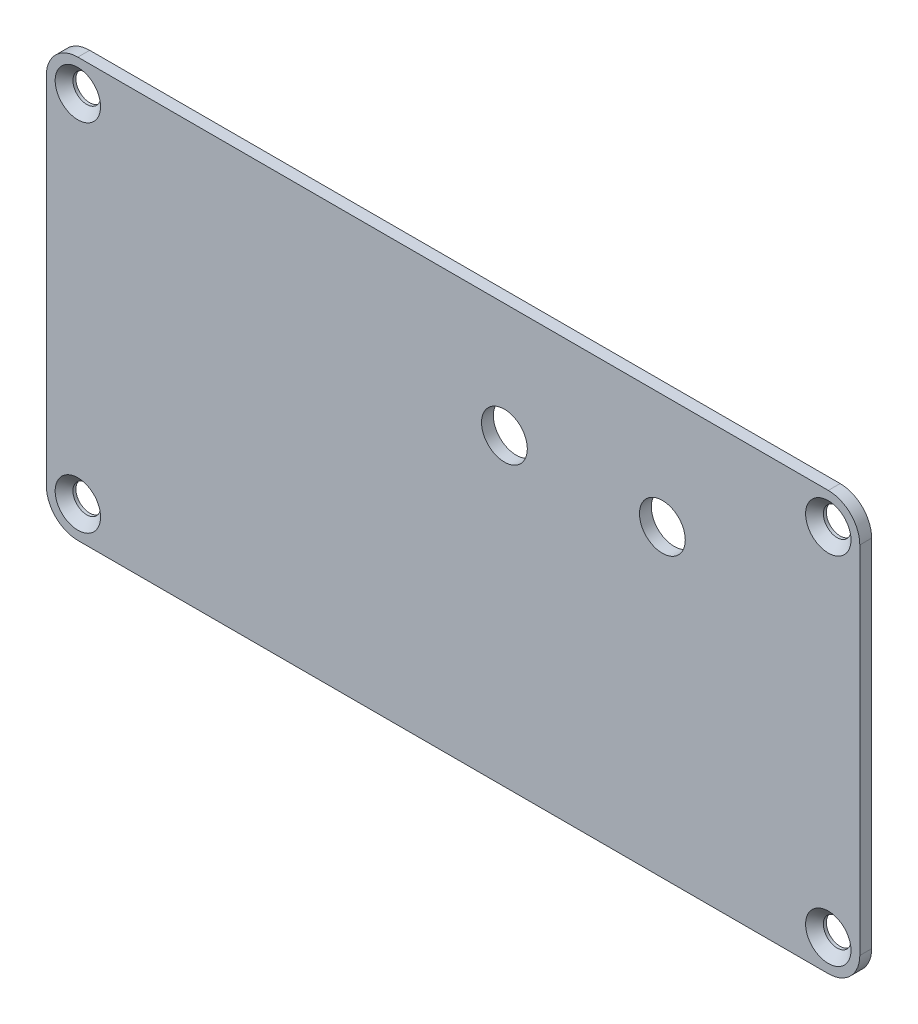
SolidWorks part; units mm, degrees
ref_plane "Plan de face" through (0, 0, 0) normal (0, 0, 1) x (1, 0, 0)
ref_plane "Plan de dessus" through (0, 0, 0) normal (0, 1, 0) x (1, 0, 0)
ref_plane "Plan de droite" through (0, 0, 0) normal (1, 0, 0) x (0, 0, -1)
ref_plane "Plan1" through (0, 0, -0.75) normal (0, 0, -1) x (-1, 0, 0)
sketch "Esquisse1" plane through (0, 0, -0.75) normal (0, 0, -1) x (-1, 0, 0)
  line L0 (-51.5, -26.5) -> (51.5, -26.5)
  line L1 (51.5, -26.5) -> (51.5, 26.5)
  line L2 (51.5, 26.5) -> (-51.5, 26.5)
  line L3 (-51.5, 26.5) -> (-51.5, -26.5)
extrude "Boss.-Extru.1" add sketch "Esquisse1" against normal blind 1.5
hole_wizard "Fraisage pour vis à tête fraisée M31" positions "Esquisse3" profile "Esquisse2" countersink size "M3" standard "Ansi Metric"
sketch "Esquisse3" plane through (0, 0, 0.75) normal (0, 0, 1) x (1, 0, 0)
  point P0 (-47.51, 22.5)
  point P1 (47.51, 22.5)
  point P2 (47.51, -22.5)
  point P3 (-47.51, -22.5)
sketch "Esquisse2" plane through (-47.51, 22.5, 0.75) normal (1, 0, 0) x (0, -1, 0)
  line L0 (0, 0) -> (0, 1.5)
  line L1 (0, 1.5) -> (1.75, 1.5)
  line L2 (1.75, 1.5) -> (1.75, 1.125)
  line L3 (1.75, 1.125) -> (2.875, 0)
  line L5 (2.875, 0) -> (0, 0)
  line L6 (-1.75, 1.125) -> (-2.875, 0) construction
  line L11 (0, -6.35) -> (0, 107.95) construction
  dimension "Diamètre du perçage jusqu'au prochain" = 3.5
  dimension "Profondeur du perçage jusqu'au prochain" = 1.5
  dimension "Diamètre du fraisage entrant" = 5.75
  dimension "Angle du fraisage entrant" = 90
fillet "Congé1" radius 3.99 4 edges at (51.5, 26.5, 0) (51.5, -26.5, 0) (-51.5, 26.5, 0) (-51.5, -26.5, 0)
sketch "Esquisse4" plane through (0, 0, 0.75) normal (0, 0, 1) x (1, 0, 0)
  line L0 (0, -26.5) -> (0, 26.5) construction
  line L1 (47.51, -26.5) -> (-47.51, -26.5) construction
  line L2 (-47.51, 26.5) -> (47.51, 26.5) construction
  line L3 (-51.5, 0) -> (51.5, 0) construction
  line L6 (-51.5, -22.51) -> (-51.5, 22.51) construction
  line L7 (51.5, 22.51) -> (51.5, -22.51) construction
  circle A0 centre (26.5, 12) radius 2.9
  circle A1 centre (6.5, 12) radius 2.9
  dimension "D1" = 5.8
  dimension "D3" = 12
  dimension "D2" = 25
  dimension "D4" = 20
extrude "Enlèv. mat.-Extru.1" cut sketch "Esquisse4" against normal through all
